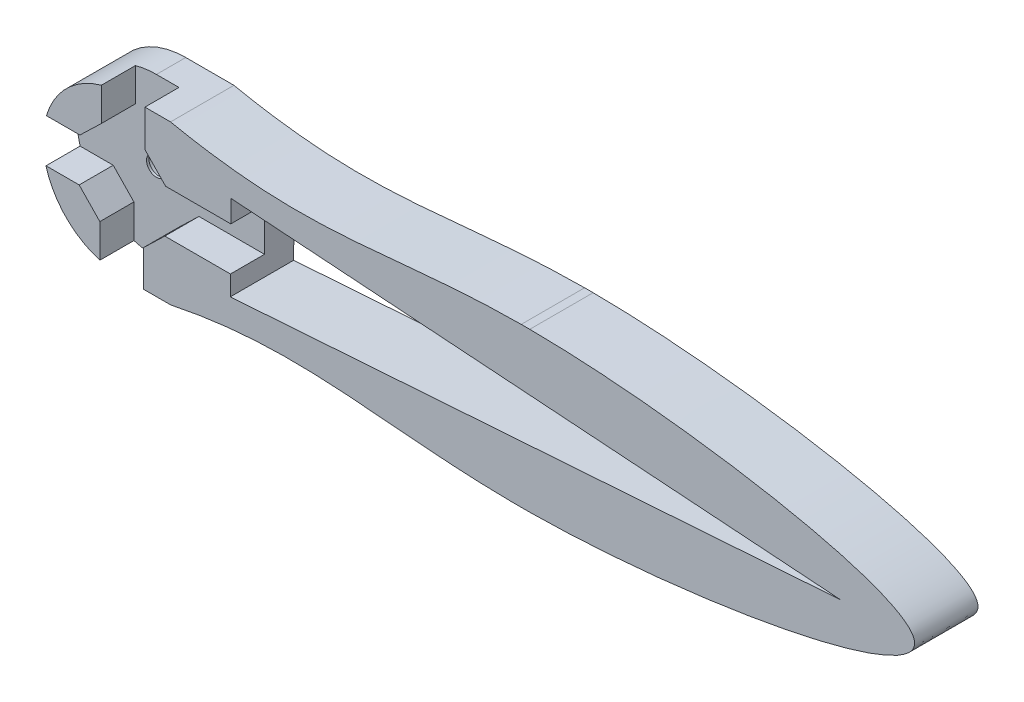
SolidWorks part; units mm, degrees
ref_plane "Plan de face" through (0, 0, 0) normal (0, 0, 1) x (1, 0, 0)
ref_plane "Plan de dessus" through (0, 0, 0) normal (0, 1, 0) x (1, 0, 0)
ref_plane "Plan de droite" through (0, 0, 0) normal (1, 0, 0) x (0, 0, -1)
sketch "Esquisse1" plane through (0, 0, 0) normal (0, 0, 1) x (1, 0, 0)
  line L0 (50, -10.9971) -> (50, 26.1419) construction
  line L1 (0, 0) -> (100, 0)
  line L3 (0, 20) -> (100, 20)
  arc A0 (0, 0) -> (0, 20) centre (0, 10) cw
  arc A1 (100, 0) -> (100, 20) centre (100, 10) ccw
  point P9 (50, 0)
  point P11 (50, 20)
  dimension "D3" = 10
  dimension "D1" = 20
  dimension "D2" = 50
extrude "Boss.-Extru.1" add sketch "Esquisse1" along normal blind 8
sketch "Esquisse13" plane through (0, 0, 8) normal (0, 0, 1) x (1, 0, 0)
  circle A0 centre (0, 10) radius 4
  arc A1 (0, 20) -> (0, 0) centre (0, 10) ccw construction
  dimension "D1" = 8
extrude "Enlèv. mat.-Extru.9" cut sketch "Esquisse13" against normal blind 4.3
sketch "Esquisse14" plane through (0, 0, 8) normal (0, 0, 1) x (1, 0, 0)
  line L0 (2.6554, 4.5441) -> (2.6554, -2.0086)
  line L1 (-2.6554, 22.0086) -> (2.8446, 21.9124)
  line L2 (-2.8446, -1.9124) -> (-2.8446, 4.6403)
  line L3 (12.0086, 12.6554) -> (17.8181, 12.6554)
  line L4 (17.8181, 12.6554) -> (17.8181, 7.1554)
  line L5 (17.8181, 7.1554) -> (11.9124, 7.1554)
  line L7 (2.6554, -2.0086) -> (-2.8446, -1.9124)
  line L10 (-12.0086, 7.3446) -> (-11.9124, 12.8446)
  line L12 (5.4559, 12.6554) -> (2.8446, 15.3597)
  line L13 (2.6554, 4.5441) -> (5.3597, 7.1554)
  line L14 (-2.6554, 15.4559) -> (-5.3597, 12.8446)
  line L15 (-5.4559, 7.3446) -> (-2.8446, 4.6403)
  line L16 (5.3597, 7.1554) -> (11.9124, 7.1554)
  line L17 (5.4559, 12.6554) -> (12.0086, 12.6554)
  line L18 (2.8446, 15.3597) -> (2.8446, 21.9124)
  line L19 (-2.6554, 15.4559) -> (-2.6554, 22.0086)
  line L20 (-5.3597, 12.8446) -> (-11.9124, 12.8446)
  line L21 (-5.4559, 7.3446) -> (-12.0086, 7.3446)
  circle A3 centre (0, 10) radius 6.0678 construction
  dimension "D1" = 5.5
  dimension "D2" = 6.5527
extrude "Enlèv. mat.-Extru.10" cut sketch "Esquisse14" against normal blind 4.3
sketch "Esquisse15" plane through (0, 0, 0) normal (0, 0, -1) x (-1, 0, 0)
  circle A0 centre (0, 10) radius 2.5
  arc A1 (0, 0) -> (0, 20) centre (0, 10) ccw construction
  dimension "D1" = 5
extrude "Enlèv. mat.-Extru.11" cut sketch "Esquisse15" against normal blind 3.4
sketch "Esquisse16" plane through (0, 0, 3.4) normal (0, 0, -1) x (-1, 0, 0)
  circle A0 centre (0, 10) radius 1.25
  circle A1 centre (0, 10) radius 2.5 construction
  dimension "D1" = 2.5
extrude "Enlèv. mat.-Extru.12" cut sketch "Esquisse16" against normal up to next
sketch "Esquisse17" plane through (0, 0, 8) normal (0, 0, 1) x (1, 0, 0)
  line L0 (6.0787, 20) -> (100, 0) construction
  line L1 (100, 0) -> (100, 20) construction
  line L2 (100, 20) -> (6.0787, 0) construction
  line L3 (2.6554, 0) -> (100, 0) construction
  line L5 (6.0787, 0) -> (6.0787, 20) construction
  line L6 (6.0787, 20) -> (100, 10) construction
  line L7 (51.4223, 50.7744) -> (51.4223, -35.7761) construction
  line L8 (100, 10) -> (6.0787, 0) construction
  line L9 (100, 20) -> (2.8446, 20) construction
  spline S0 degree 3 poles (-23.1517, 28.6346) (19.5298, 13.689) (43.7729, 24.4596) (129.1726, 9.9553) (44.5396, -4.2884) (17.5692, 5.7323) (-18.3293, -7.4175) (-23.1517, 28.6346) (19.5298, 13.689) (43.7729, 24.4596) knots -0.235665 -0.132702 -0.109136 0 0.182524 0.382168 0.581811 0.764335 0.867298 0.890864 1 1.182524 1.382168 1.581811 only from (6.0787, 20) to (6.0787, 20)
extrude "Enlèv. mat.-Extru.13" cut sketch "Esquisse17" against normal blind 10 flip side to cut
sketch "Esquisse18" plane through (0, 0, 8) normal (0, 0, 1) x (1, 0, 0)
  line L0 (-2.8446, 4.6403) -> (30.0773, 4.6403) construction
  line L1 (-2.6554, 15.4559) -> (30.0773, 15.4559) construction
  line L2 (13.6163, 4.6403) -> (13.711, 15.4559) construction
  line L3 (13.6163, 4.6403) -> (13.711, 15.4559)
  line L4 (13.711, 15.4559) -> (90.6551, 10.0481)
  line L5 (90.6551, 10.0481) -> (13.6163, 4.6403)
extrude "Enlèv. mat.-Extru.14" cut sketch "Esquisse18" against normal blind 10
